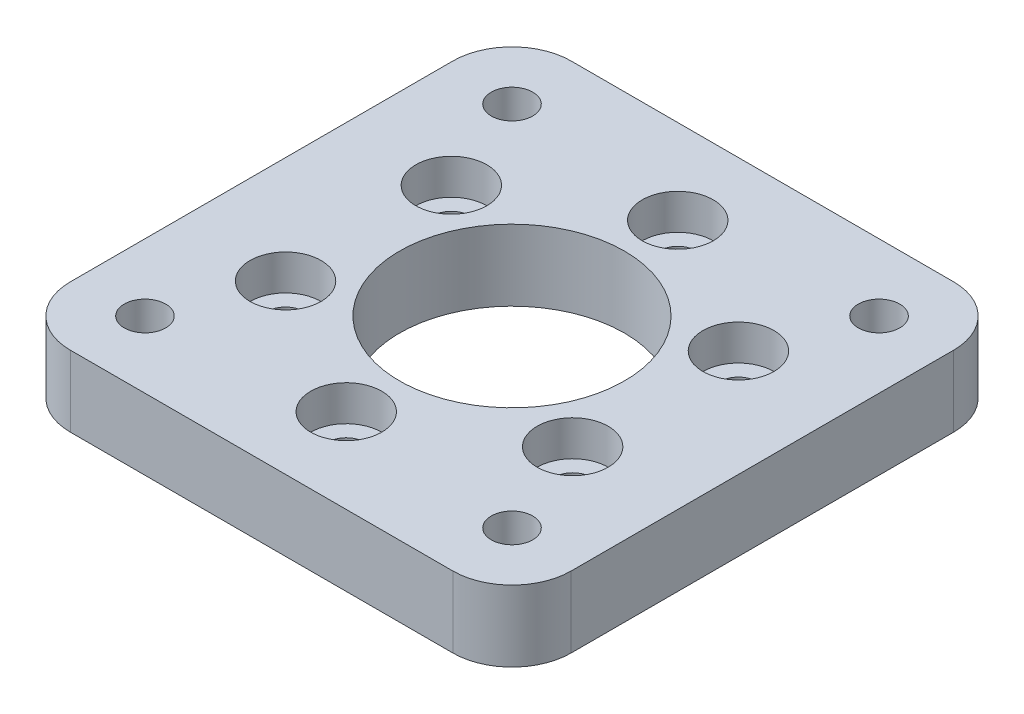
SolidWorks part; units mm, degrees
ref_plane "Front Plane" through (0, 0, 0) normal (0, 0, 1) x (1, 0, 0)
ref_plane "Top Plane" through (0, 0, 0) normal (0, 1, 0) x (1, 0, 0)
ref_plane "Right Plane" through (0, 0, 0) normal (1, 0, 0) x (0, 0, -1)
sketch "Sketch1" plane through (0, 0, 0) normal (0, 1, 0) x (1, 0, 0)
  line L1 (-21.15, 21.15) -> (21.15, 21.15)
  line L2 (-21.15, 21.15) -> (-21.15, -21.15)
  line L3 (-21.15, -21.15) -> (21.15, -21.15)
  line L4 (21.15, 21.15) -> (21.15, -21.15)
  line L5 (-21.15, 21.15) -> (21.15, -21.15) construction
  line L6 (-21.15, -21.15) -> (21.15, 21.15) construction
  point P0 (0, 0)
  dimension "D1" = 42.3
  dimension "D2" = 42.3
extrude "Boss-Extrude1" add sketch "Sketch1" along normal mid plane 6
fillet "Fillet1" radius 5 4 edges at (-21.15, 0, 21.15) (-21.15, 0, -21.15) (21.15, 0, -21.15) (21.15, 0, 21.15)
sketch "Sketch2" plane through (0, -3, 0) normal (0, -1, 0) x (1, 0, 0)
  line L1 (-15.5, -15.5) -> (15.5, -15.5) construction
  line L2 (-15.5, -15.5) -> (-15.5, 15.5) construction
  line L3 (-15.5, 15.5) -> (15.5, 15.5) construction
  line L4 (15.5, -15.5) -> (15.5, 15.5) construction
  line L5 (-15.5, -15.5) -> (15.5, 15.5) construction
  line L6 (-15.5, 15.5) -> (15.5, -15.5) construction
  circle A0 centre (-15.5, 15.5) radius 1.75
  circle A1 centre (15.5, 15.5) radius 1.75
  circle A2 centre (15.5, -15.5) radius 1.75
  circle A3 centre (-15.5, -15.5) radius 1.75
  point P0 (0, 0)
  dimension "D3" = 3.5
  dimension "D4" = 3.5
  dimension "D5" = 3.5
  dimension "D6" = 3.5
  dimension "D1" = 31
  dimension "D2" = 31
extrude "Cut-Extrude1" cut sketch "Sketch2" against normal through all
sketch "Sketch4" plane through (0, -3, 0) normal (0, -1, 0) x (1, 0, 0)
  circle A0 centre (0, 0) radius 9.5
  dimension "D1" = 19
extrude "Cut-Extrude3" cut sketch "Sketch4" against normal through all
sketch "Sketch5" plane through (0, 3, 0) normal (0, 1, 0) x (1, 0, 0)
  line L0 (0, 0) -> (0, 21.15) construction
  line L1 (16.15, 21.15) -> (-16.15, 21.15) construction
  circle A0 centre (0, 14) radius 1.55
  dimension "D1" = 3.1
  dimension "D2" = 14
extrude "Cut-Extrude4" cut sketch "Sketch5" against normal through all
sketch "Sketch6" plane through (0, 3, 0) normal (0, 1, 0) x (1, 0, 0)
  circle A0 centre (0, 14) radius 3
  dimension "D1" = 6
extrude "Cut-Extrude5" cut sketch "Sketch6" against normal blind 3
pattern_circular "CirPattern1" count 6 every 60 about axis through (0, 0, 0) along (0, 1, 0) of "Cut-Extrude4", "Cut-Extrude5"
